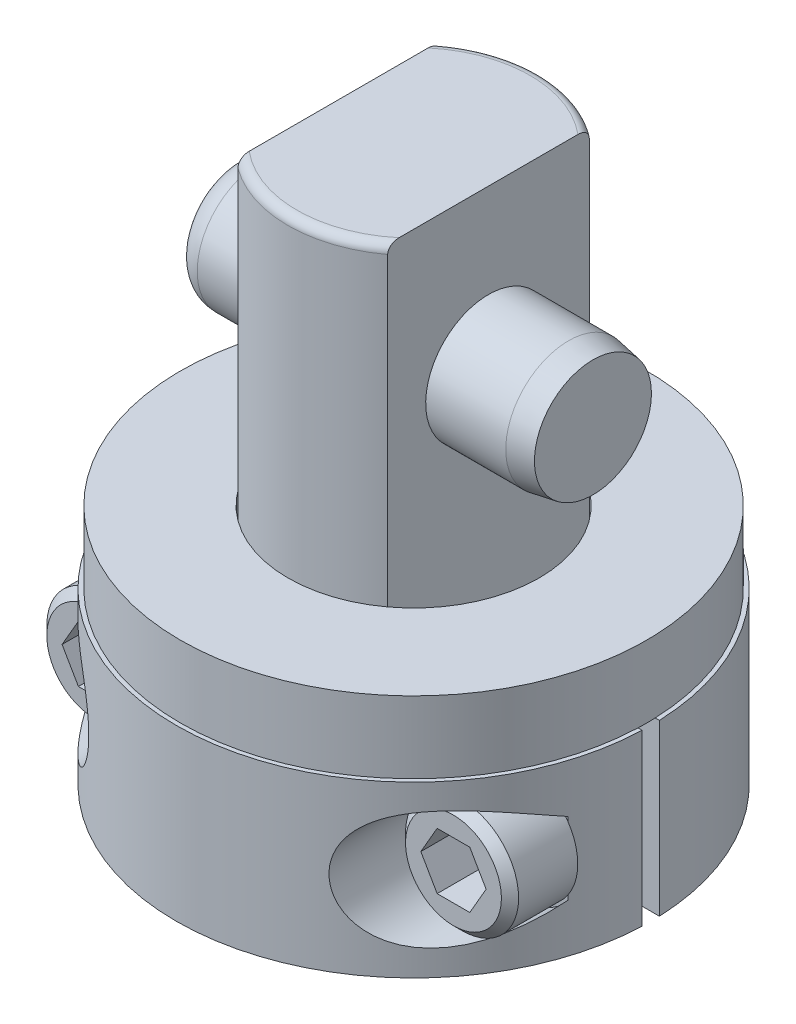
SolidWorks part; units mm, degrees
material "Alloy Steel"
ref_plane "Front Plane" through (0, 0, 0) normal (0, 0, 1) x (1, 0, 0)
ref_plane "Top Plane" through (0, 0, 0) normal (0, 1, 0) x (1, 0, 0)
ref_plane "Right Plane" through (0, 0, 0) normal (1, 0, 0) x (0, 0, -1)
sketch "Sketch1" plane through (0, 0, 0) normal (1, 0, 0) x (0, 0, -1)
  line L0 (0, 41.656) -> (11.1125, 41.656)
  line L1 (11.1125, 41.656) -> (11.1125, 1.1684)
  line L2 (11.1125, 1.1684) -> (5.9944, 1.1684)
  line L3 (5.9944, 1.1684) -> (5.9944, -11.5316)
  line L4 (5.9944, -11.5316) -> (0, -11.5316)
  line L5 (0, -11.5316) -> (0, 41.656)
  line L6 (0, -15.3594) -> (0, 43.147) construction
  dimension "D1" = 53.1876
  dimension "D2" = 12.7
  dimension "D3" = 11.9888
  dimension "D4" = 22.225
  dimension "D5" = 1.1684
revolve "Revolve1" add sketch "Sketch1" angle 360 about L6
fillet "Fillet1" radius 0.7874 1 edges at (0, 41.656, -11.1125)
sketch "Sketch2" plane through (0, 0, 0) normal (0, 0, 1) x (1, 0, 0)
  line L0 (6.6294, 41.656) -> (11.1125, 41.656)
  line L1 (11.1125, 41.656) -> (11.1125, 8.7884)
  line L2 (11.1125, 8.7884) -> (6.6294, 8.7884)
  line L3 (6.6294, 8.7884) -> (6.6294, 41.656)
  line L4 (-11.1125, 41.656) -> (-6.6294, 41.656)
  line L5 (-6.6294, 41.656) -> (-6.6294, 8.7884)
  line L6 (-6.6294, 8.7884) -> (-11.1125, 8.7884)
  line L7 (-11.1125, 8.7884) -> (-11.1125, 41.656)
  line L8 (0, 5.9766) -> (0, 42.131) construction
  line L9 (10.3251, 41.656) -> (-10.3251, 41.656) construction
  line L10 (11.1125, 1.1684) -> (11.1125, 40.8686) construction
  line L11 (-11.1125, 40.8686) -> (-11.1125, 1.1684) construction
  dimension "D1" = 13.2588
  dimension "D2" = 32.8676
extrude "Cut-Extrude1" cut sketch "Sketch2" against normal through all and the other way through all
sketch "Sketch3" plane through (0, 1.1684, 0) normal (0, -1, 0) x (1, 0, 0)
  circle A0 centre (0, 0) radius 4.8895
  circle A1 centre (0, 0) radius 5.9944 construction
  circle A2 centre (0, 0) radius 5.9944
  dimension "D1" = 9.779
extrude "Cut-Extrude2" cut sketch "Sketch3" along normal blind 2.54
chamfer "Chamfer1" distance 0.762 angle 45 1 edges at (0, -11.5316, -5.9944)
sketch "Sketch4" plane through (0, 0, 0) normal (1, 0, 0) x (0, 0, -1)
  line L0 (-11.1125, 1.1684) -> (11.1125, 1.1684) construction
  circle A0 centre (0, 27.7876) radius 5.5588
  dimension "D1" = 11.1176
  dimension "D2" = 26.6192
extrude "Extrude1" add sketch "Sketch4" along normal mid plane 31.75
chamfer "Chamfer2" distance 0.381 angle 80 1 edges at (15.875, 27.7876, -5.5588)
fillet "Fillet2" radius 2.286 1 edges at (-15.875, 27.7876, -5.5588)
sketch "Sketch5" plane through (0, 0, 0) normal (0, 1, 0) x (1, 0, 0)
  line L0 (11.0863, 0.762) -> (20.992, 0.762)
  line L1 (11.0863, -0.762) -> (20.992, -0.762)
  line L2 (-11.0863, -0.762) -> (-20.992, -0.762)
  line L3 (-11.0863, 0.762) -> (-20.992, 0.762)
  line L4 (0, 0) -> (24.3028, 0) construction
  arc A0 (20.992, 0.762) -> (-20.992, 0.762) centre (0, 0) ccw
  arc A1 (-20.992, -0.762) -> (20.992, -0.762) centre (0, 0) ccw
  arc A2 (11.0863, 0.762) -> (-11.0863, 0.762) centre (0, 0) ccw
  arc A3 (-11.0863, -0.762) -> (11.0863, -0.762) centre (0, 0) ccw
  circle A4 centre (0, 0) radius 11.1125 construction
  dimension "D2" = 21.0058
  dimension "D1" = 1.524
extrude "Extrude2" add sketch "Sketch5" along normal blind 7.5057 and the other way blind 7.5057
sketch "Sketch6" plane through (0, 0, 0.762) normal (0, 0, 1) x (1, 0, 0)
  line L0 (0, -5.6718) -> (0, 5.6718) construction
  line L1 (-20.992, -7.5057) -> (20.992, -7.5057) construction
  circle A0 centre (15.875, 0) radius 5.2451
  circle A1 centre (-15.875, 0) radius 5.2451
  dimension "D1" = 10.4902
  dimension "D2" = 31.75
  dimension "D3" = 7.5057
extrude "Cut-Extrude3" cut sketch "Sketch6" along normal through all from offset 5.588
sketch "Sketch7" plane through (0, 0, 6.35) normal (0, 0, 1) x (1, 0, 0)
  circle A0 centre (15.875, 0) radius 5.0038
  circle A1 centre (-15.875, 0) radius 5.0038
  arc A3 (-20.023, -3.2101) -> (-20.023, 3.2101) centre (-15.875, 0) ccw construction
  arc A4 (20.023, 3.2101) -> (20.023, -3.2101) centre (15.875, 0) ccw construction
  dimension "D1" = 10.0076
extrude "Extrude3" add sketch "Sketch7" along normal blind 5.9944
chamfer "Chamfer3" distance 0.762 angle 45 2 edges at (-10.8712, 0, 12.3444) (20.8788, 0, 12.3444)
sketch "Sketch8" plane through (0, 0, 12.3444) normal (0, 0, 1) x (1, 0, 0)
  line L0 (0, 0) -> (0, -21.769) construction
  line L1 (17.3195, 2.5019) -> (18.7639, 0)
  line L2 (14.4305, 2.5019) -> (17.3195, 2.5019)
  line L3 (12.9861, 0) -> (14.4305, 2.5019)
  line L4 (14.4305, -2.5019) -> (12.9861, 0)
  line L5 (17.3195, -2.5019) -> (14.4305, -2.5019)
  line L6 (18.7639, 0) -> (17.3195, -2.5019)
  line L8 (-18.7639, 0) -> (-17.3195, -2.5019)
  line L9 (-17.3195, -2.5019) -> (-14.4305, -2.5019)
  line L10 (-14.4305, -2.5019) -> (-12.9861, 0)
  line L11 (-12.9861, 0) -> (-14.4305, 2.5019)
  line L12 (-14.4305, 2.5019) -> (-17.3195, 2.5019)
  line L13 (-17.3195, 2.5019) -> (-18.7639, 0)
  circle A0 centre (-15.875, 0) radius 2.5019 construction
  circle A1 centre (15.875, 0) radius 2.5019 construction
  dimension "D2" = 5.0038
extrude "Cut-Extrude4" cut sketch "Sketch8" against normal blind 5.0038
sketch "Sketch10" plane through (0, 0, 0) normal (0, 0, 1) x (1, 0, 0)
  circle A0 centre (15.875, 0) radius 2.9972
  circle A1 centre (-15.875, 0) radius 2.9972
  circle A2 centre (-15.875, 0) radius 5.0038 construction
  circle A3 centre (15.875, 0) radius 5.0038 construction
  dimension "D1" = 5.9944
extrude "Extrude4" add sketch "Sketch10" along normal up to next and the other way up to next
sketch "Sketch11" plane through (0, 7.5057, 0) normal (0, 1, 0) x (-1, 0, 0)
  circle A0 centre (0, 0) radius 20.6375
  circle A1 centre (0, 0) radius 11.1125
  circle A3 centre (0, 0) radius 5.9944 construction
  dimension "D1" = 41.275
  dimension "D2" = 22.225
extrude "Extrude5" add sketch "Sketch11" along normal blind 6.35
